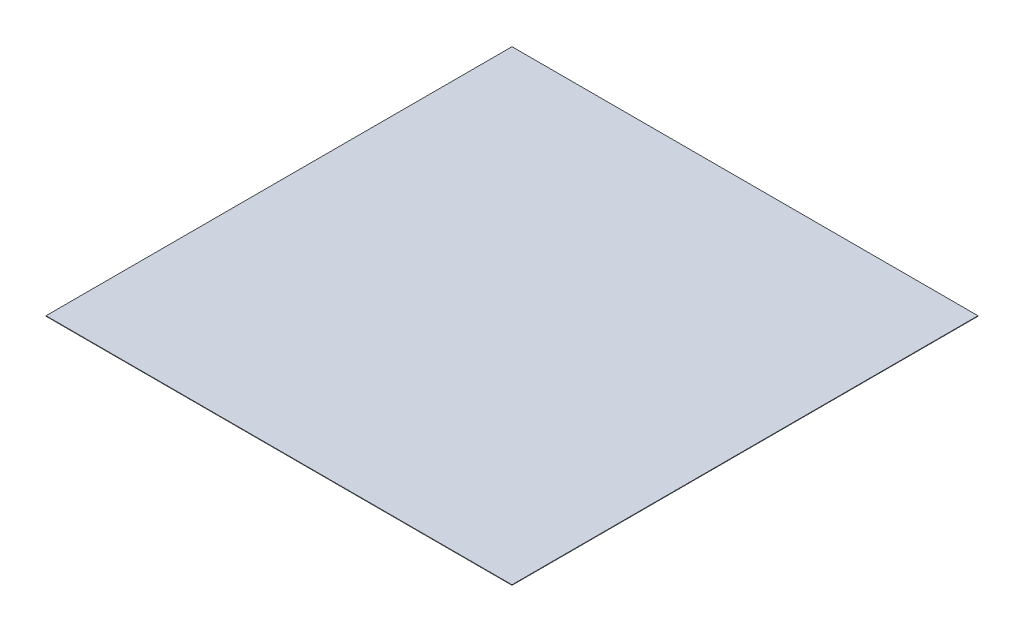
SolidWorks part; units mm, degrees
ref_plane "Plano frontal" through (0, 0, 0) normal (0, 0, 1) x (1, 0, 0)
ref_plane "Plano superior" through (0, 0, 0) normal (0, 1, 0) x (1, 0, 0)
ref_plane "Plano direito" through (0, 0, 0) normal (1, 0, 0) x (0, 0, -1)
sketch "Esboço1" plane through (0, 0, 0) normal (0, 1, 0) x (1, 0, 0)
  line L1 (-15000, -15000) -> (15000, -15000)
  line L2 (-15000, -15000) -> (-15000, 15000)
  line L3 (-15000, 15000) -> (15000, 15000)
  line L4 (15000, -15000) -> (15000, 15000)
  line L5 (-15000, -15000) -> (15000, 15000) construction
  line L6 (-15000, 15000) -> (15000, -15000) construction
  point P0 (0, 0)
  dimension "D1" = 30000
  dimension "D2" = 30000
extrude "Ressalto-extrusão1" add sketch "Esboço1" along normal blind 30
